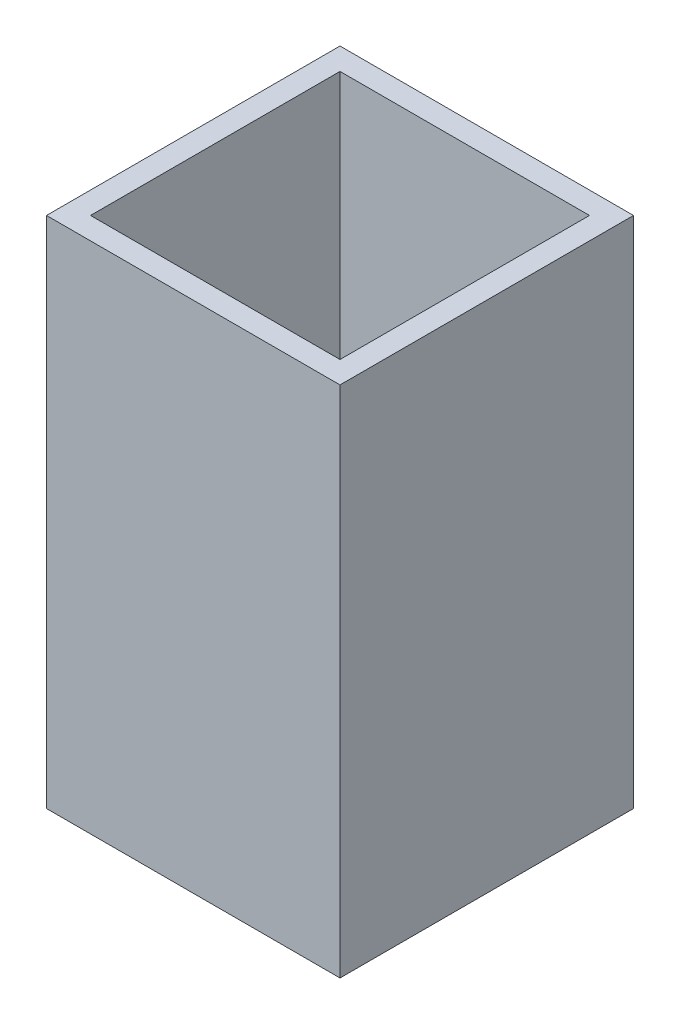
SolidWorks part; units mm, degrees
ref_plane "Front Plane" through (0, 0, 0) normal (0, 0, 1) x (1, 0, 0)
ref_plane "Top Plane" through (0, 0, 0) normal (0, 1, 0) x (1, 0, 0)
ref_plane "Right Plane" through (0, 0, 0) normal (1, 0, 0) x (0, 0, -1)
sketch "Sketch1" plane through (0, 0, 0) normal (0, 1, 0) x (1, 0, 0)
  line L0 (-8.5, 8.5) -> (8.5, 8.5)
  line L1 (-10, -10) -> (10, -10)
  line L2 (-10, -10) -> (-10, 10)
  line L3 (-10, 10) -> (10, 10)
  line L4 (10, -10) -> (10, 10)
  line L5 (-10, -10) -> (10, 10) construction
  line L6 (-10, 10) -> (10, -10) construction
  line L7 (8.5, -8.5) -> (8.5, 8.5)
  line L8 (-8.5, -8.5) -> (8.5, -8.5)
  line L9 (-8.5, -8.5) -> (-8.5, 8.5)
  point P0 (0, 0)
  dimension "D1" = 20
  dimension "D2" = 20
  dimension "D3" = 1.5
extrude "Boss-Extrude1" add sketch "Sketch1" along normal blind 35
